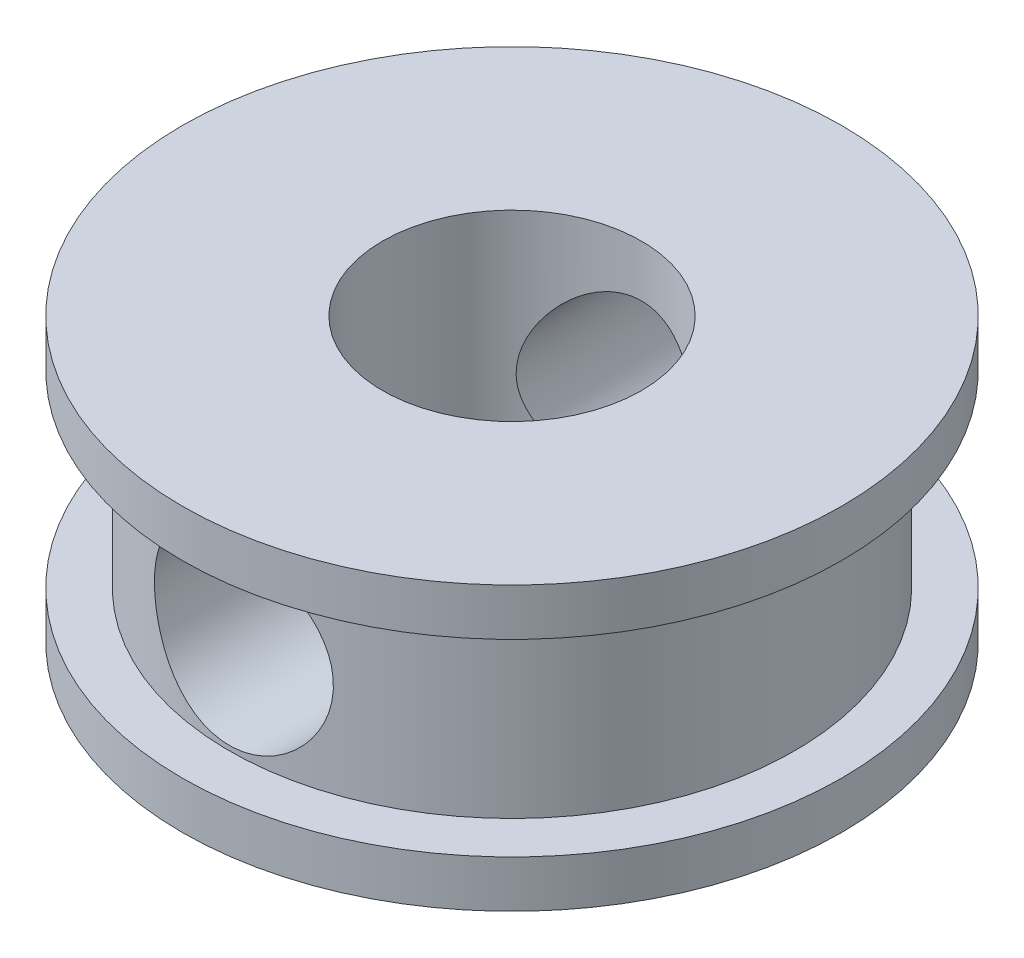
SolidWorks part; units mm, degrees
ref_plane "정면" through (0, 0, 0) normal (0, 0, 1) x (1, 0, 0)
ref_plane "윗면" through (0, 0, 0) normal (0, 1, 0) x (1, 0, 0)
ref_plane "우측면" through (0, 0, 0) normal (1, 0, 0) x (0, 0, -1)
sketch "스케치2" plane through (0, 0, 0) normal (0, 0, 1) x (1, 0, 0)
  line L1 (0, 3.2639) -> (7, 3.2639)
  line L2 (0, -2.7361) -> (7, -2.7361)
  line L3 (7, 3.2639) -> (7, 2.2639)
  line L4 (7, -2.7361) -> (7, -1.7361)
  line L5 (7, 2.2639) -> (6, 2.2639)
  line L6 (7, -1.7361) -> (6, -1.7361)
  line L7 (6, -1.7361) -> (6, 2.2639)
  line L8 (0, 3.2639) -> (0, -2.7361)
  dimension "D1" = 7
  dimension "D2" = 6
  dimension "D3" = 1
  dimension "D4" = 1
  dimension "D5" = 1
  dimension "D6" = 7
revolve "회전2" add sketch "스케치2" angle 360 about L8
sketch "스케치4" plane through (0, 0, 0) normal (0, 0, 1) x (1, 0, 0)
  line L0 (0, 3.2639) -> (0, -2.7361) construction
  circle A0 centre (0, 0.2639) radius 1.9
  dimension "D1" = 3.8
extrude "컷-돌출3" cut sketch "스케치4" along normal through all both and the other way through all
sketch "스케치5" plane through (0, 3.2639, 0) normal (0, 1, 0) x (1, 0, 0)
  circle A0 centre (0, 0) radius 2.75
  dimension "D1" = 5.5
extrude "컷-돌출4" cut sketch "스케치5" against normal blind 10 contours A0
